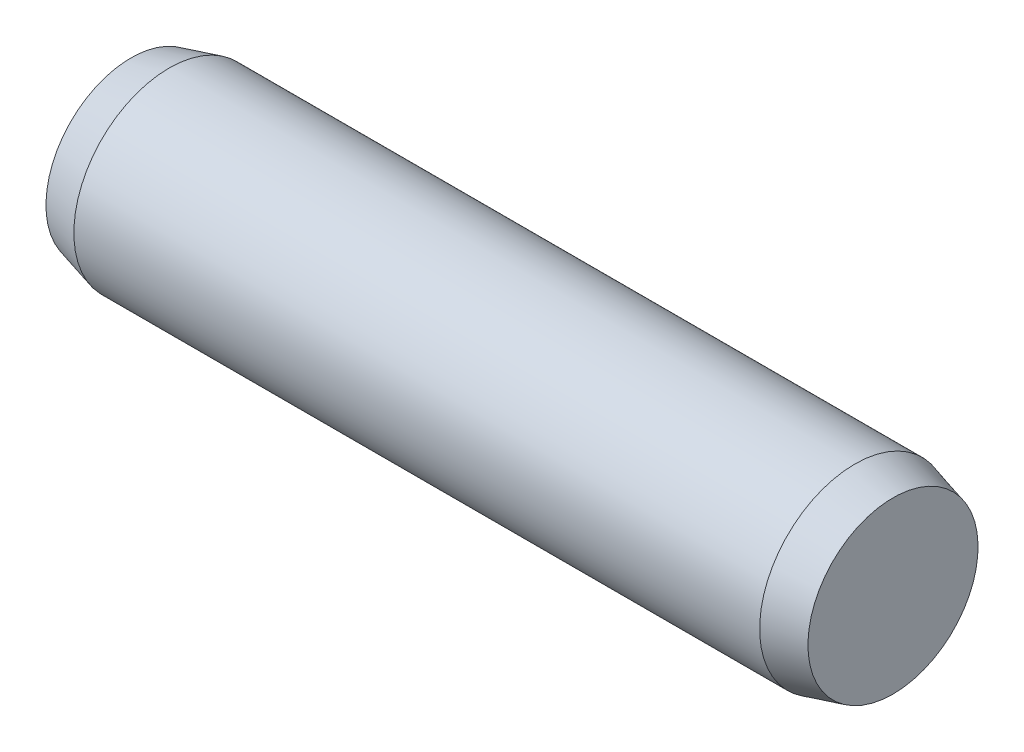
SolidWorks part; units mm, degrees
ref_plane "Front" through (0, 0, 0) normal (0, 0, 1) x (1, 0, 0)
ref_plane "Top" through (0, 0, 0) normal (0, 1, 0) x (1, 0, 0)
ref_plane "Right" through (0, 0, 0) normal (1, 0, 0) x (0, 0, -1)
sketch "Support-Front" plane through (0, 0, 0) normal (0, 0, 1) x (1, 0, 0)
  line L0 (0.6, 0) -> (6, 0) construction
  line L1 (0, 0.6696) -> (0.3, 0.75)
  line L2 (0, -0.6696) -> (0.3, -0.75)
  line L3 (0.3, 0.75) -> (5.7, 0.75)
  line L4 (0.3, -0.75) -> (5.7, -0.75)
  line L5 (0.3, 0.75) -> (0.3, -0.75) construction
  line L6 (6, -0.75) -> (6, 0.75) construction
  line L7 (6, 0.75) -> (5.7, 0.75) construction
  line L8 (6, -0.75) -> (5.7, -0.75) construction
  line L9 (5.7, 0.75) -> (5.7, -0.75) construction
  line L10 (0.6, 0) -> (0.3, 0) construction
  line L11 (0.3, 0) -> (0, 0) construction
  line L12 (0.3, 0) -> (0, 0.6696) construction
  line L13 (0, 0.6696) -> (0, -0.6696)
  line L14 (5.7, 0.75) -> (6, 0.6696)
  line L15 (6, 0.6696) -> (6, -0.6696)
  line L16 (5.7, -0.75) -> (6, -0.6696)
  line L17 (6, 0.5768) -> (5.9, 0.5768) construction
  line L18 (5.9, 0.5768) -> (5.8, 0.5768) construction
  line L19 (5.8, 0.5768) -> (5.7, 0.5768) construction
  line L20 (5.9, 0.5768) -> (5.9, 0) construction
  line L21 (5.7, 0.75) -> (6, 0.5768) construction
  arc A2 (6, 0.5768) -> (6, -0.5768) centre (7.6135, 0) ccw
  dimension "D1" = 15
  dimension "Diam" = 1.5
  dimension "Length" = 6
  dimension "Length-Chamfer-Front" = 0.3
  dimension "Length-Chamfer-Back" = 0.3
  dimension "D2" = 15
  dimension "D3" = 30
sketch "Sketch2" plane through (0, 0, 0) normal (0, 0, 1) x (1, 0, 0)
  line L9 (0.6, 0) -> (6, 0) construction
  line L12 (6, 0.6696) -> (6, -0.6696) construction
  line L14 (5.7, 0.75) -> (6, 0.6696) construction
  line L15 (0.3, 0.75) -> (5.7, 0.75) construction
  line L16 (0, 0.6696) -> (0.3, 0.75) construction
  line L17 (0, 0.6696) -> (0, -0.6696) construction
  line L18 (0, 0) -> (6, 0) construction
  line L19 (6, 0.6696) -> (6, 0)
  line L20 (5.7, 0.75) -> (6, 0.6696)
  line L21 (0.3, 0.75) -> (5.7, 0.75)
  line L22 (0, 0.6696) -> (0.3, 0.75)
  line L23 (0, 0.6696) -> (0, 0)
  line L24 (6, 0) -> (0, 0)
revolve "Body" add sketch "Sketch2" angle 360 about L18
sketch "Sketch3" plane through (0, 0, 0) normal (0, 0, 1) x (1, 0, 0)
  line L0 (0.6, 0) -> (6, 0) construction
  line L1 (6, 0.6696) -> (6, -0.6696) construction
  line L2 (5.9, 0) -> (6, 0) construction
  line L3 (6, 0.5768) -> (6, 0)
  line L4 (6, 0) -> (5.9, 0)
  arc A0 (6, 0.5768) -> (6, -0.5768) centre (7.6135, 0) ccw construction
  arc A1 (6, 0.5768) -> (5.9, 0) centre (7.6135, 0) ccw
revolve "Cut-Body" [suppressed] cut sketch "Sketch3" angle 360 about L2
equation "\"Length-Chamfer-Back@Support-Front\" = \"Length-Chamfer-Front@Support-Front\""
